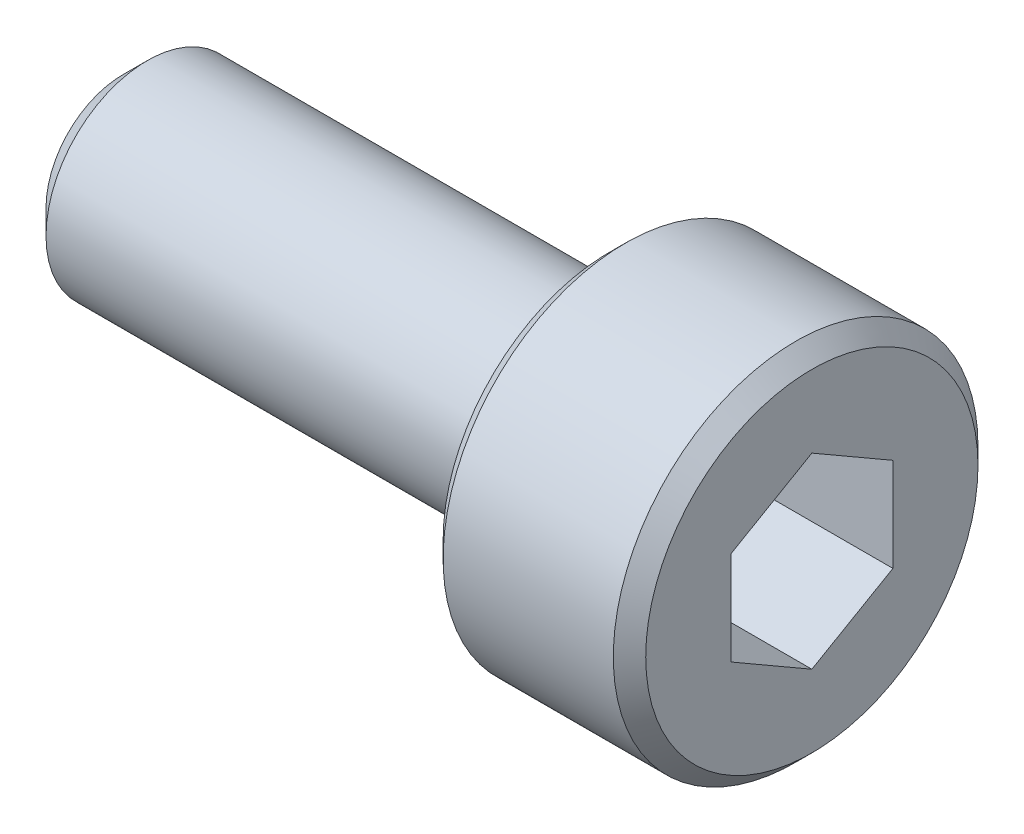
SolidWorks part; units mm, degrees
ref_plane "Front Plane" through (0, 0, 0) normal (0, 0, 1) x (1, 0, 0)
ref_plane "Top Plane" through (0, 0, 0) normal (0, 1, 0) x (1, 0, 0)
ref_plane "Right Plane" through (0, 0, 0) normal (1, 0, 0) x (0, 0, -1)
sketch "Sketch1" plane through (0, 0, 0) normal (0, 1, 0) x (1, 0, 0)
  line L1 (0, 0) -> (-6, 0)
  line L2 (0, 0) -> (0, -1.25)
  line L3 (0, -1.25) -> (-6, -1.25)
  line L4 (-6, 0) -> (-6, -1.25)
  line L5 (0, -1.25) -> (2.5, -1.25)
  line L6 (0, -1.25) -> (0, 1)
  line L7 (0, 1) -> (2.5, 1)
  line L8 (2.5, -1.25) -> (2.5, 1)
  dimension "D1" = 1.25
  dimension "D2" = 2.25
  dimension "D3" = 2.5
  dimension "D4" = 6
revolve "Revolve1" add sketch "Sketch1" angle 360 about L3
ref_point "Point1"
sketch "Sketch3" plane through (2.5, 0, 0) normal (1, 0, 0) x (0, 0, -1)
  line L1 (-1.25, 1.1547) -> (-2.25, 0.5774)
  line L2 (-2.25, 0.5774) -> (-2.25, -0.5774)
  line L3 (-2.25, -0.5774) -> (-1.25, -1.1547)
  line L4 (-1.25, -1.1547) -> (-0.25, -0.5774)
  line L5 (-0.25, -0.5774) -> (-0.25, 0.5774)
  line L6 (-0.25, 0.5774) -> (-1.25, 1.1547)
  circle A0 centre (-1.25, 0) radius 1 construction
  dimension "D1" = 2
extrude "Cut-Extrude1" cut sketch "Sketch3" against normal blind 2
chamfer "Chamfer1" distance 0.2 angle 45 2 edges at (0, 0, -1) (2.5, 0, -1)
chamfer "Chamfer2" distance 0.3 angle 45 1 edges at (-6, 0, 0)
